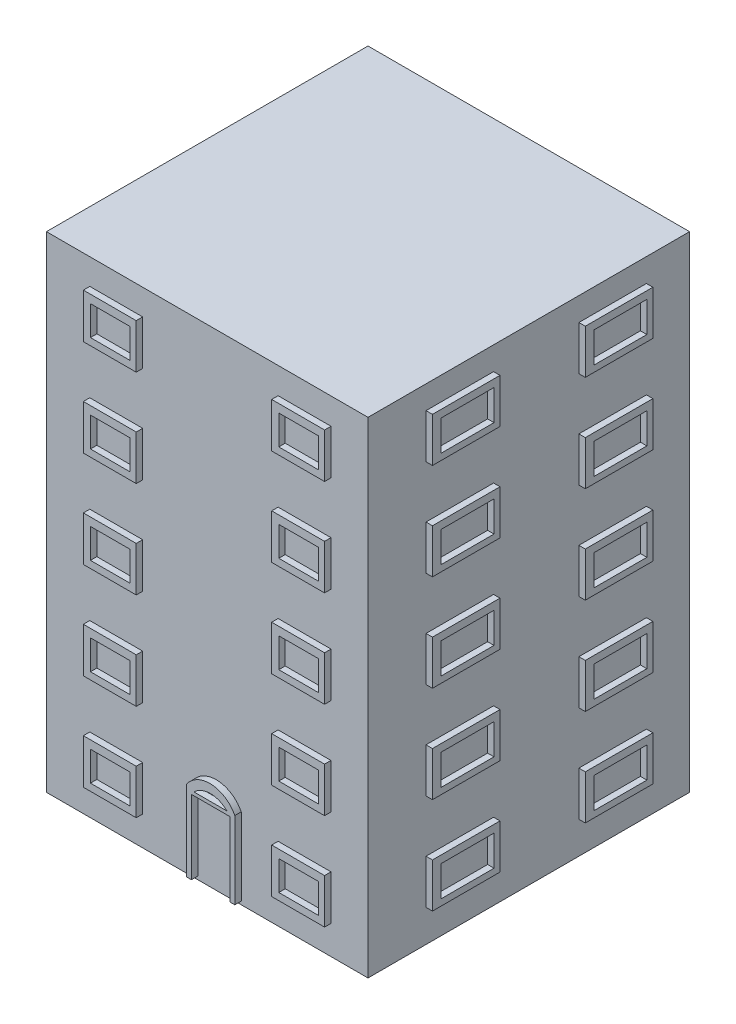
SolidWorks part; units mm, degrees
ref_plane "Plano frontal" through (0, 0, 0) normal (0, 0, 1) x (1, 0, 0)
ref_plane "Plano superior" through (0, 0, 0) normal (0, 1, 0) x (1, 0, 0)
ref_plane "Plano direito" through (0, 0, 0) normal (1, 0, 0) x (0, 0, -1)
sketch "Esboço1" plane through (0, 0, 0) normal (0, 1, 0) x (1, 0, 0)
  line L1 (-1, -0.5) -> (0, -0.5)
  line L2 (-1, -0.5) -> (-1, 0.5)
  line L3 (-1, 0.5) -> (0, 0.5)
  line L4 (0, -0.5) -> (0, 0.5)
  line L5 (-1, -0.5) -> (0, 0.5) construction
  line L6 (-1, 0.5) -> (0, -0.5) construction
  point P0 (0, 0)
  point P6 (0, 0)
  dimension "D1" = 1
extrude "Ressalto-extrusão1" add sketch "Esboço1" along normal blind 0.01
sketch "Esboço2" plane through (0, 0.01, 0) normal (0, 1, 0) x (1, 0, 0)
  line L4 (0, -0.5) -> (0, 0.5)
  line L5 (-1, -0.5) -> (0, -0.5)
  line L6 (-1, 0.5) -> (-1, -0.5)
  line L7 (0, 0.5) -> (-1, 0.5)
extrude "Ressalto-extrusão2" add sketch "Esboço2" along normal blind 1.5
sketch "Esboço3" plane through (0, 0, 0) normal (1, 0, 0) x (0, 0, -1)
  line L0 (-0.5, 0.01) -> (0.5, 0.01) construction
  line L1 (-0.5, 1.51) -> (-0.5, 0) construction
  line L2 (0.5, 1.51) -> (0.5, 0) construction
  line L3 (-0.5, 0) -> (0.5, 0) construction
  line L4 (-0.5, 0.31) -> (0.5, 0.31) construction
  line L5 (-0.5, 0.61) -> (0.5, 0.61) construction
  line L6 (-0.5, 0.91) -> (0.5, 0.91) construction
  line L7 (-0.5, 1.21) -> (0.5, 1.21) construction
  line L8 (0.1558, 0.2374) -> (0.3658, 0.2374)
  line L9 (-0.3196, 0.2378) -> (-0.1095, 0.2378)
  line L10 (-0.3196, 0.2378) -> (-0.3196, 0.1)
  line L11 (-0.3196, 0.1) -> (-0.1095, 0.1)
  line L12 (-0.1095, 0.2378) -> (-0.1095, 0.1)
  line L13 (-0.2922, 0.2145) -> (-0.1281, 0.2145)
  line L14 (-0.2922, 0.2145) -> (-0.2922, 0.1197)
  line L15 (-0.2922, 0.1197) -> (-0.1281, 0.1197)
  line L16 (-0.1281, 0.2145) -> (-0.1281, 0.1197)
  line L17 (0.1558, 0.2374) -> (0.1558, 0.0997)
  line L18 (0.1558, 0.0997) -> (0.3658, 0.0997)
  line L19 (0.3658, 0.2374) -> (0.3658, 0.0997)
  line L20 (0.1831, 0.2141) -> (0.3473, 0.2141)
  line L21 (0.1831, 0.2141) -> (0.1831, 0.1193)
  line L22 (0.1831, 0.1193) -> (0.3473, 0.1193)
  line L23 (0.3473, 0.2141) -> (0.3473, 0.1193)
  line L24 (0.1558, 0.5374) -> (0.3658, 0.5374)
  line L25 (-0.3196, 0.5378) -> (-0.1095, 0.5378)
  line L26 (-0.3196, 0.5378) -> (-0.3196, 0.4)
  line L27 (-0.3196, 0.4) -> (-0.1095, 0.4)
  line L28 (-0.1095, 0.5378) -> (-0.1095, 0.4)
  line L29 (-0.2922, 0.5145) -> (-0.1281, 0.5145)
  line L30 (-0.2922, 0.5145) -> (-0.2922, 0.4197)
  line L31 (-0.2922, 0.4197) -> (-0.1281, 0.4197)
  line L32 (-0.1281, 0.5145) -> (-0.1281, 0.4197)
  line L33 (0.1558, 0.5374) -> (0.1558, 0.3997)
  line L34 (0.1558, 0.3997) -> (0.3658, 0.3997)
  line L35 (0.3658, 0.5374) -> (0.3658, 0.3997)
  line L36 (0.1831, 0.5141) -> (0.3473, 0.5141)
  line L37 (0.1831, 0.5141) -> (0.1831, 0.4193)
  line L38 (0.1831, 0.4193) -> (0.3473, 0.4193)
  line L39 (0.3473, 0.5141) -> (0.3473, 0.4193)
  line L40 (0.1558, 0.8374) -> (0.3658, 0.8374)
  line L41 (-0.3196, 0.8378) -> (-0.1095, 0.8378)
  line L42 (-0.3196, 0.8378) -> (-0.3196, 0.7)
  line L43 (-0.3196, 0.7) -> (-0.1095, 0.7)
  line L44 (-0.1095, 0.8378) -> (-0.1095, 0.7)
  line L45 (-0.2922, 0.8145) -> (-0.1281, 0.8145)
  line L46 (-0.2922, 0.8145) -> (-0.2922, 0.7197)
  line L47 (-0.2922, 0.7197) -> (-0.1281, 0.7197)
  line L48 (-0.1281, 0.8145) -> (-0.1281, 0.7197)
  line L49 (0.1558, 0.8374) -> (0.1558, 0.6997)
  line L50 (0.1558, 0.6997) -> (0.3658, 0.6997)
  line L51 (0.3658, 0.8374) -> (0.3658, 0.6997)
  line L52 (0.1831, 0.8141) -> (0.3473, 0.8141)
  line L53 (0.1831, 0.8141) -> (0.1831, 0.7193)
  line L54 (0.1831, 0.7193) -> (0.3473, 0.7193)
  line L55 (0.3473, 0.8141) -> (0.3473, 0.7193)
  line L56 (0.1558, 1.1374) -> (0.3658, 1.1374)
  line L57 (-0.3196, 1.1378) -> (-0.1095, 1.1378)
  line L58 (-0.3196, 1.1378) -> (-0.3196, 1)
  line L59 (-0.3196, 1) -> (-0.1095, 1)
  line L60 (-0.1095, 1.1378) -> (-0.1095, 1)
  line L61 (-0.2922, 1.1145) -> (-0.1281, 1.1145)
  line L62 (-0.2922, 1.1145) -> (-0.2922, 1.0197)
  line L63 (-0.2922, 1.0197) -> (-0.1281, 1.0197)
  line L64 (-0.1281, 1.1145) -> (-0.1281, 1.0197)
  line L65 (0.1558, 1.1374) -> (0.1558, 0.9997)
  line L66 (0.1558, 0.9997) -> (0.3658, 0.9997)
  line L67 (0.3658, 1.1374) -> (0.3658, 0.9997)
  line L68 (0.1831, 1.1141) -> (0.3473, 1.1141)
  line L69 (0.1831, 1.1141) -> (0.1831, 1.0193)
  line L70 (0.1831, 1.0193) -> (0.3473, 1.0193)
  line L71 (0.3473, 1.1141) -> (0.3473, 1.0193)
  line L72 (0.1558, 1.4374) -> (0.3658, 1.4374)
  line L73 (-0.3196, 1.4378) -> (-0.1095, 1.4378)
  line L74 (-0.3196, 1.4378) -> (-0.3196, 1.3)
  line L75 (-0.3196, 1.3) -> (-0.1095, 1.3)
  line L76 (-0.1095, 1.4378) -> (-0.1095, 1.3)
  line L77 (-0.2922, 1.4145) -> (-0.1281, 1.4145)
  line L78 (-0.2922, 1.4145) -> (-0.2922, 1.3197)
  line L79 (-0.2922, 1.3197) -> (-0.1281, 1.3197)
  line L80 (-0.1281, 1.4145) -> (-0.1281, 1.3197)
  line L81 (0.1558, 1.4374) -> (0.1558, 1.2997)
  line L82 (0.1558, 1.2997) -> (0.3658, 1.2997)
  line L83 (0.3658, 1.4374) -> (0.3658, 1.2997)
  line L84 (0.1831, 1.4141) -> (0.3473, 1.4141)
  line L85 (0.1831, 1.4141) -> (0.1831, 1.3193)
  line L86 (0.1831, 1.3193) -> (0.3473, 1.3193)
  line L87 (0.3473, 1.4141) -> (0.3473, 1.3193)
  dimension "D1" = 0.01
  dimension "D2" = 0.3
  dimension "D4" = 0.09
  dimension "D3" = 4
  dimension "D5" = 5
sketch "Esboço4" plane through (0, 0, 0.5) normal (0, 0, 1) x (1, 0, 0)
  line L0 (0, 0.31) -> (-1, 0.31) construction
  line L1 (-1, 1.51) -> (-1, 0) construction
  line L3 (-0.5441, 0.01) -> (-0.3941, 0.01)
  line L4 (-0.5441, 0.01) -> (-0.5441, 0.26)
  line L6 (-0.3941, 0.01) -> (-0.3941, 0.2505)
  line L7 (-0.5212, 0.2505) -> (-0.4188, 0.2505)
  line L8 (-0.5291, 0.24) -> (-0.4091, 0.24)
  line L9 (-0.5291, 0.24) -> (-0.5291, 0.01)
  line L10 (-0.5291, 0.01) -> (-0.4091, 0.01)
  line L11 (-0.4091, 0.24) -> (-0.4091, 0.01)
  line L12 (-0.1151, 0.2284) -> (-0.2795, 0.2284)
  line L13 (-0.7008, 0.23) -> (-0.8652, 0.23)
  line L14 (-0.7008, 0.23) -> (-0.7008, 0.0912)
  line L15 (-0.7008, 0.0912) -> (-0.8652, 0.0912)
  line L16 (-0.8652, 0.23) -> (-0.8652, 0.0912)
  line L17 (-0.8432, 0.2046) -> (-0.7194, 0.2046)
  line L18 (-0.8432, 0.2046) -> (-0.8432, 0.1132)
  line L19 (-0.8432, 0.1132) -> (-0.7194, 0.1132)
  line L20 (-0.7194, 0.2046) -> (-0.7194, 0.1132)
  line L29 (-0.1151, 0.2284) -> (-0.1151, 0.0895)
  line L30 (-0.1151, 0.0895) -> (-0.2795, 0.0895)
  line L31 (-0.2795, 0.2284) -> (-0.2795, 0.0895)
  line L32 (-0.2575, 0.203) -> (-0.1337, 0.203)
  line L33 (-0.2575, 0.203) -> (-0.2575, 0.1116)
  line L34 (-0.2575, 0.1116) -> (-0.1337, 0.1116)
  line L35 (-0.1337, 0.203) -> (-0.1337, 0.1116)
  line L100 (-0.7008, 0.53) -> (-0.8652, 0.53)
  line L101 (-0.7008, 0.53) -> (-0.7008, 0.3912)
  line L102 (-0.7008, 0.3912) -> (-0.8652, 0.3912)
  line L103 (-0.8652, 0.53) -> (-0.8652, 0.3912)
  line L104 (-0.8432, 0.5046) -> (-0.7194, 0.5046)
  line L105 (-0.8432, 0.5046) -> (-0.8432, 0.4132)
  line L106 (-0.8432, 0.4132) -> (-0.7194, 0.4132)
  line L107 (-0.7194, 0.5046) -> (-0.7194, 0.4132)
  line L108 (-0.1151, 0.5284) -> (-0.2795, 0.5284)
  line L109 (-0.1151, 0.5284) -> (-0.1151, 0.3895)
  line L110 (-0.1151, 0.3895) -> (-0.2795, 0.3895)
  line L111 (-0.2795, 0.5284) -> (-0.2795, 0.3895)
  line L112 (-0.2575, 0.503) -> (-0.1337, 0.503)
  line L113 (-0.2575, 0.503) -> (-0.2575, 0.4116)
  line L114 (-0.2575, 0.4116) -> (-0.1337, 0.4116)
  line L115 (-0.1337, 0.503) -> (-0.1337, 0.4116)
  line L116 (-0.7008, 0.83) -> (-0.8652, 0.83)
  line L117 (-0.7008, 0.83) -> (-0.7008, 0.6912)
  line L118 (-0.7008, 0.6912) -> (-0.8652, 0.6912)
  line L119 (-0.8652, 0.83) -> (-0.8652, 0.6912)
  line L120 (-0.8432, 0.8046) -> (-0.7194, 0.8046)
  line L121 (-0.8432, 0.8046) -> (-0.8432, 0.7132)
  line L122 (-0.8432, 0.7132) -> (-0.7194, 0.7132)
  line L123 (-0.7194, 0.8046) -> (-0.7194, 0.7132)
  line L124 (-0.1151, 0.8284) -> (-0.2795, 0.8284)
  line L125 (-0.1151, 0.8284) -> (-0.1151, 0.6895)
  line L126 (-0.1151, 0.6895) -> (-0.2795, 0.6895)
  line L127 (-0.2795, 0.8284) -> (-0.2795, 0.6895)
  line L128 (-0.2575, 0.803) -> (-0.1337, 0.803)
  line L129 (-0.2575, 0.803) -> (-0.2575, 0.7116)
  line L130 (-0.2575, 0.7116) -> (-0.1337, 0.7116)
  line L131 (-0.1337, 0.803) -> (-0.1337, 0.7116)
  line L132 (-0.7008, 1.13) -> (-0.8652, 1.13)
  line L133 (-0.7008, 1.13) -> (-0.7008, 0.9912)
  line L134 (-0.7008, 0.9912) -> (-0.8652, 0.9912)
  line L135 (-0.8652, 1.13) -> (-0.8652, 0.9912)
  line L136 (-0.8432, 1.1046) -> (-0.7194, 1.1046)
  line L137 (-0.8432, 1.1046) -> (-0.8432, 1.0132)
  line L138 (-0.8432, 1.0132) -> (-0.7194, 1.0132)
  line L139 (-0.7194, 1.1046) -> (-0.7194, 1.0132)
  line L140 (-0.1151, 1.1284) -> (-0.2795, 1.1284)
  line L141 (-0.1151, 1.1284) -> (-0.1151, 0.9895)
  line L142 (-0.1151, 0.9895) -> (-0.2795, 0.9895)
  line L143 (-0.2795, 1.1284) -> (-0.2795, 0.9895)
  line L144 (-0.2575, 1.103) -> (-0.1337, 1.103)
  line L145 (-0.2575, 1.103) -> (-0.2575, 1.0116)
  line L146 (-0.2575, 1.0116) -> (-0.1337, 1.0116)
  line L147 (-0.1337, 1.103) -> (-0.1337, 1.0116)
  line L148 (-0.7008, 1.43) -> (-0.8652, 1.43)
  line L149 (-0.7008, 1.43) -> (-0.7008, 1.2912)
  line L150 (-0.7008, 1.2912) -> (-0.8652, 1.2912)
  line L151 (-0.8652, 1.43) -> (-0.8652, 1.2912)
  line L152 (-0.8432, 1.4046) -> (-0.7194, 1.4046)
  line L153 (-0.8432, 1.4046) -> (-0.8432, 1.3132)
  line L154 (-0.8432, 1.3132) -> (-0.7194, 1.3132)
  line L155 (-0.7194, 1.4046) -> (-0.7194, 1.3132)
  line L156 (-0.1151, 1.4284) -> (-0.2795, 1.4284)
  line L157 (-0.1151, 1.4284) -> (-0.1151, 1.2895)
  line L158 (-0.1151, 1.2895) -> (-0.2795, 1.2895)
  line L159 (-0.2795, 1.4284) -> (-0.2795, 1.2895)
  line L160 (-0.2575, 1.403) -> (-0.1337, 1.403)
  line L161 (-0.2575, 1.403) -> (-0.2575, 1.3116)
  line L162 (-0.2575, 1.3116) -> (-0.1337, 1.3116)
  line L163 (-0.1337, 1.403) -> (-0.1337, 1.3116)
  line L164 (-1, 0) -> (0, 0) construction
  arc A0 (-0.5441, 0.26) -> (-0.3941, 0.2505) centre (-0.472, 0.2106) cw
  arc A2 (-0.5212, 0.2505) -> (-0.4188, 0.2505) centre (-0.47, 0.1993) cw
  point P9 (0, 0)
  point P10 (0, 0)
  point P35 (0, 0)
  dimension "D1" = 0.25
  dimension "D2" = 0.01
  dimension "D3" = 0.12
  dimension "D4" = 0.23
extrude "Ressalto-extrusão3" add sketch "Esboço3" along normal blind 0.02
sketch "Esboço5" plane through (-1, 0, 0) normal (-1, 0, 0) x (0, 0, 1)
  line L0 (0.5, 0.31) -> (-0.5, 0.31) construction
  line L1 (-0.5, 1.51) -> (-0.5, 0) construction
  line L2 (-0.32, 0.2278) -> (-0.1099, 0.2278)
  line L3 (-0.32, 0.2278) -> (-0.32, 0.09)
  line L4 (-0.32, 0.09) -> (-0.1099, 0.09)
  line L5 (-0.1099, 0.2278) -> (-0.1099, 0.09)
  line L6 (-0.2926, 0.2045) -> (-0.1285, 0.2045)
  line L7 (-0.2926, 0.2045) -> (-0.2926, 0.1097)
  line L8 (-0.2926, 0.1097) -> (-0.1285, 0.1097)
  line L9 (-0.1285, 0.2045) -> (-0.1285, 0.1097)
  line L10 (-0.5, 0) -> (0.5, 0) construction
  line L11 (0.1601, 0.2286) -> (0.3779, 0.2286)
  line L12 (0.1601, 0.2286) -> (0.1601, 0.0908)
  line L13 (0.1601, 0.0908) -> (0.3779, 0.0908)
  line L14 (0.3779, 0.2286) -> (0.3779, 0.0908)
  line L15 (0.1876, 0.2053) -> (0.3518, 0.2053)
  line L16 (0.1876, 0.2053) -> (0.1876, 0.1105)
  line L17 (0.1876, 0.1105) -> (0.3518, 0.1105)
  line L18 (0.3518, 0.2053) -> (0.3518, 0.1105)
  line L19 (-0.1099, 0.09) -> (0.4356, 0.09) construction
  line L20 (-0.32, 0.5278) -> (-0.1099, 0.5278)
  line L21 (-0.32, 0.5278) -> (-0.32, 0.39)
  line L22 (-0.32, 0.39) -> (-0.1099, 0.39)
  line L23 (-0.1099, 0.5278) -> (-0.1099, 0.39)
  line L24 (-0.2926, 0.5045) -> (-0.1285, 0.5045)
  line L25 (-0.2926, 0.5045) -> (-0.2926, 0.4097)
  line L26 (-0.2926, 0.4097) -> (-0.1285, 0.4097)
  line L27 (-0.1285, 0.5045) -> (-0.1285, 0.4097)
  line L28 (0.1601, 0.5286) -> (0.3779, 0.5286)
  line L29 (0.1601, 0.5286) -> (0.1601, 0.3908)
  line L30 (0.1601, 0.3908) -> (0.3779, 0.3908)
  line L31 (0.3779, 0.5286) -> (0.3779, 0.3908)
  line L32 (0.1876, 0.5053) -> (0.3518, 0.5053)
  line L33 (0.1876, 0.5053) -> (0.1876, 0.4105)
  line L34 (0.1876, 0.4105) -> (0.3518, 0.4105)
  line L35 (0.3518, 0.5053) -> (0.3518, 0.4105)
  line L36 (-0.1099, 0.39) -> (0.4356, 0.39) construction
  line L37 (-0.32, 0.8278) -> (-0.1099, 0.8278)
  line L38 (-0.32, 0.8278) -> (-0.32, 0.69)
  line L39 (-0.32, 0.69) -> (-0.1099, 0.69)
  line L40 (-0.1099, 0.8278) -> (-0.1099, 0.69)
  line L41 (-0.2926, 0.8045) -> (-0.1285, 0.8045)
  line L42 (-0.2926, 0.8045) -> (-0.2926, 0.7097)
  line L43 (-0.2926, 0.7097) -> (-0.1285, 0.7097)
  line L44 (-0.1285, 0.8045) -> (-0.1285, 0.7097)
  line L45 (0.1601, 0.8286) -> (0.3779, 0.8286)
  line L46 (0.1601, 0.8286) -> (0.1601, 0.6908)
  line L47 (0.1601, 0.6908) -> (0.3779, 0.6908)
  line L48 (0.3779, 0.8286) -> (0.3779, 0.6908)
  line L49 (0.1876, 0.8053) -> (0.3518, 0.8053)
  line L50 (0.1876, 0.8053) -> (0.1876, 0.7105)
  line L51 (0.1876, 0.7105) -> (0.3518, 0.7105)
  line L52 (0.3518, 0.8053) -> (0.3518, 0.7105)
  line L53 (-0.1099, 0.69) -> (0.4356, 0.69) construction
  line L54 (-0.32, 1.1278) -> (-0.1099, 1.1278)
  line L55 (-0.32, 1.1278) -> (-0.32, 0.99)
  line L56 (-0.32, 0.99) -> (-0.1099, 0.99)
  line L57 (-0.1099, 1.1278) -> (-0.1099, 0.99)
  line L58 (-0.2926, 1.1045) -> (-0.1285, 1.1045)
  line L59 (-0.2926, 1.1045) -> (-0.2926, 1.0097)
  line L60 (-0.2926, 1.0097) -> (-0.1285, 1.0097)
  line L61 (-0.1285, 1.1045) -> (-0.1285, 1.0097)
  line L62 (0.1601, 1.1286) -> (0.3779, 1.1286)
  line L63 (0.1601, 1.1286) -> (0.1601, 0.9908)
  line L64 (0.1601, 0.9908) -> (0.3779, 0.9908)
  line L65 (0.3779, 1.1286) -> (0.3779, 0.9908)
  line L66 (0.1876, 1.1053) -> (0.3518, 1.1053)
  line L67 (0.1876, 1.1053) -> (0.1876, 1.0105)
  line L68 (0.1876, 1.0105) -> (0.3518, 1.0105)
  line L69 (0.3518, 1.1053) -> (0.3518, 1.0105)
  line L70 (-0.1099, 0.99) -> (0.4356, 0.99) construction
  line L71 (-0.32, 1.4278) -> (-0.1099, 1.4278)
  line L72 (-0.32, 1.4278) -> (-0.32, 1.29)
  line L73 (-0.32, 1.29) -> (-0.1099, 1.29)
  line L74 (-0.1099, 1.4278) -> (-0.1099, 1.29)
  line L75 (-0.2926, 1.4045) -> (-0.1285, 1.4045)
  line L76 (-0.2926, 1.4045) -> (-0.2926, 1.3097)
  line L77 (-0.2926, 1.3097) -> (-0.1285, 1.3097)
  line L78 (-0.1285, 1.4045) -> (-0.1285, 1.3097)
  line L79 (0.1601, 1.4286) -> (0.3779, 1.4286)
  line L80 (0.1601, 1.4286) -> (0.1601, 1.2908)
  line L81 (0.1601, 1.2908) -> (0.3779, 1.2908)
  line L82 (0.3779, 1.4286) -> (0.3779, 1.2908)
  line L83 (0.1876, 1.4053) -> (0.3518, 1.4053)
  line L84 (0.1876, 1.4053) -> (0.1876, 1.3105)
  line L85 (0.1876, 1.3105) -> (0.3518, 1.3105)
  line L86 (0.3518, 1.4053) -> (0.3518, 1.3105)
  line L87 (-0.1099, 1.29) -> (0.4356, 1.29) construction
  dimension "D1" = 0.09
  dimension "D2" = 0.0197
  dimension "D3" = 0.0274
  dimension "D4" = 0.0233
  dimension "D5" = 0.0186
  dimension "D6" = 0.18
  dimension "D7" = 0.1641
  dimension "D8" = 0.2101
  dimension "D9" = 0.27
extrude "Ressalto-extrusão5" add sketch "Esboço4" along normal blind 0.02 contours A0 L4 L3 L9 L8 L11 L6 L7 A2 | L12 L31 L30 L29 L32 L35 L34 L33 | L13 L16 L15 L14 L17 L20 L19 L18 | L100 L103 L102 L101 L104 L107 L106 L105 | L108 L111 L110 L109 L112 L115 L114 L113 | L116 L119 L118 L117 L120 L123 L122 L121 | L124 L127 L126 L125 L128 L131 L130 L129 | L140 L143 L142 L141 L144 L147 L146 L145 | L132 L135 L134 L133 L136 L139 L138 L137 | L156 L159 L158 L157 L160 L163 L162 L161 | L155 L152 L153 L154 | L149 L150 L151 L148
extrude "Ressalto-extrusão6" add sketch "Esboço5" along normal blind 0.02
